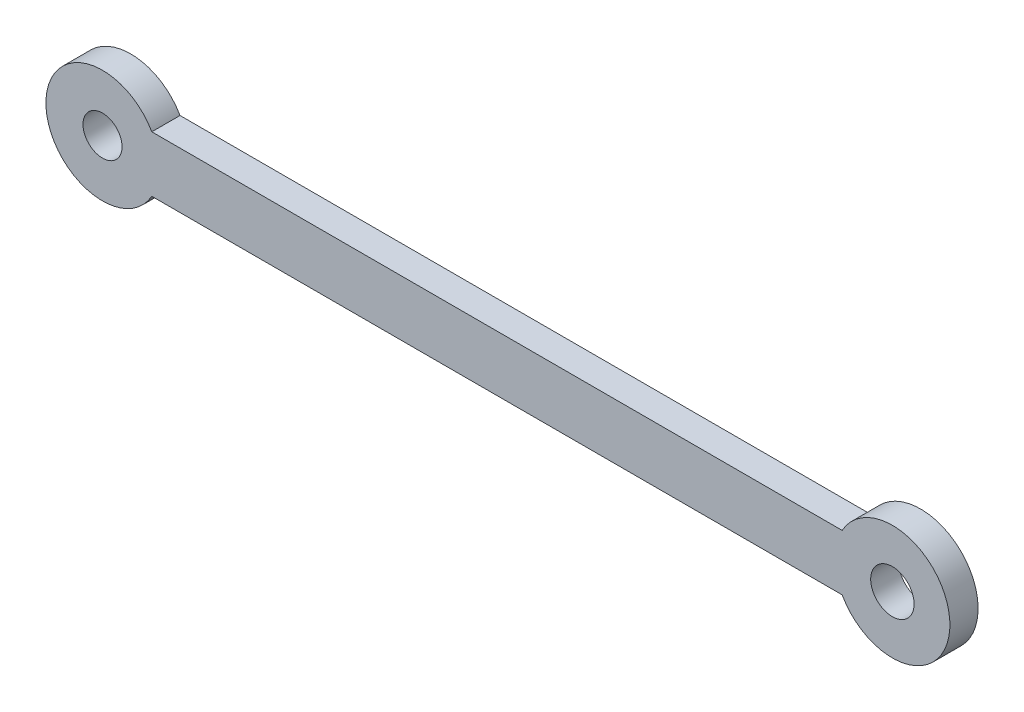
SolidWorks part; units mm, degrees
ref_plane "Front Plane" through (0, 0, 0) normal (0, 0, 1) x (1, 0, 0)
ref_plane "Top Plane" through (0, 0, 0) normal (0, 1, 0) x (1, 0, 0)
ref_plane "Right Plane" through (0, 0, 0) normal (1, 0, 0) x (0, 0, -1)
sketch "Sketch1" plane through (0, 0, 0) normal (0, 0, 1) x (1, 0, 0)
  line L0 (-51.974, 17.7247) -> (25.6465, 17.7247)
  line L2 (25.6465, 11.4472) -> (-51.974, 11.4472)
  arc A0 (-51.974, 17.7247) -> (-51.974, 11.4472) centre (-57.513, 14.586) ccw
  arc A1 (25.6465, 11.4472) -> (25.6465, 17.7247) centre (31.2952, 14.586) ccw
  circle A2 centre (-57.513, 14.586) radius 2.1935
  circle A3 centre (31.2952, 14.586) radius 2.4402
extrude "Boss-Extrude1" add sketch "Sketch1" along normal blind 3.175
